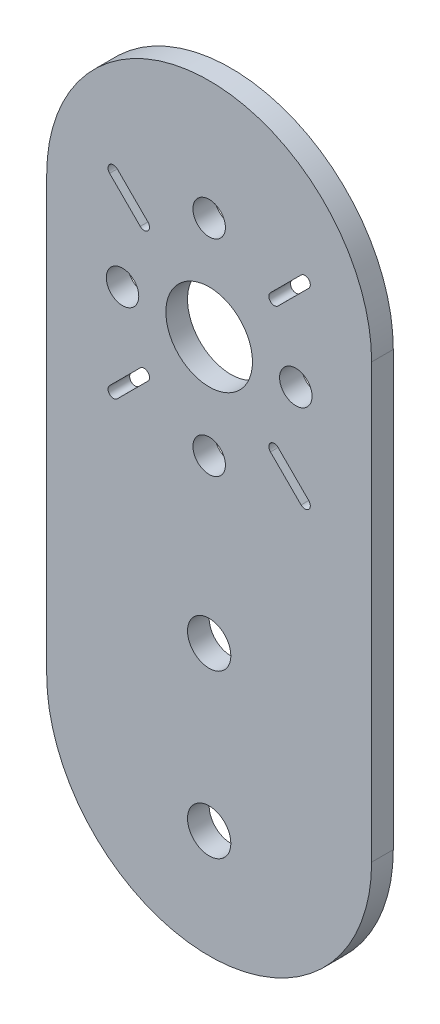
SolidWorks part; units mm, degrees
ref_plane "Front Plane" through (0, 0, 0) normal (0, 0, 1) x (1, 0, 0)
ref_plane "Top Plane" through (0, 0, 0) normal (0, 1, 0) x (1, 0, 0)
ref_plane "Right Plane" through (0, 0, 0) normal (1, 0, 0) x (0, 0, -1)
sketch "Sketch1" plane through (0, 0, 0) normal (0, 0, 1) x (1, 0, 0)
  line L2 (-15, 20) -> (-15, -20)
  line L4 (15, 20) -> (15, -20)
  line L6 (5.6569, 8.136) -> (8.4853, 5.3076)
  line L7 (6.364, 8.8431) -> (9.1924, 6.0147)
  line L8 (-6.364, 8.8431) -> (-9.1924, 6.0147)
  line L11 (6.364, 20.1569) -> (9.1924, 22.9853)
  line L12 (5.6569, 20.864) -> (8.4853, 23.6924)
  line L13 (-5.6569, 8.136) -> (-8.4853, 5.3076)
  line L14 (-5.6569, 20.864) -> (-8.4853, 23.6924)
  line L15 (-6.364, 20.1569) -> (-9.1924, 22.9853)
  arc A0 (15, 20) -> (-15, 20) centre (0, 20) ccw
  arc A1 (-15, -20) -> (15, -20) centre (0, -20) ccw
  circle A2 centre (0, -25) radius 2
  circle A3 centre (0, -10) radius 2
  circle A4 centre (0, 5) radius 1.5
  circle A5 centre (0, 24) radius 1.5
  circle A6 centre (-8, 14.5) radius 1.5
  circle A7 centre (8, 14.5) radius 1.5
  circle A8 centre (0, 14.5) radius 4
  arc A9 (5.6569, 20.864) -> (6.364, 20.1569) centre (6.0104, 20.5104) ccw
  arc A10 (9.1924, 22.9853) -> (8.4853, 23.6924) centre (8.8388, 23.3388) ccw
  arc A11 (6.364, 8.8431) -> (5.6569, 8.136) centre (6.0104, 8.4896) ccw
  arc A12 (8.4853, 5.3076) -> (9.1924, 6.0147) centre (8.8388, 5.6612) ccw
  arc A13 (-5.6569, 8.136) -> (-6.364, 8.8431) centre (-6.0104, 8.4896) ccw
  arc A14 (-9.1924, 6.0147) -> (-8.4853, 5.3076) centre (-8.8388, 5.6612) ccw
  arc A15 (-6.364, 20.1569) -> (-5.6569, 20.864) centre (-6.0104, 20.5104) ccw
  arc A16 (-8.4853, 23.6924) -> (-9.1924, 22.9853) centre (-8.8388, 23.3388) ccw
  point P0 (0, 0)
  point P10 (0, -35)
  point P24 (10.6066, 25.1066)
  point P25 (0.3536, 14.1464)
  point P26 (10.9602, 24.753)
  point P27 (-0.3536, 14.8536)
  point P28 (10.253, 25.4602)
  dimension "D3" = 10
  dimension "D4" = 15
  dimension "D5" = 15
  dimension "D7" = 16
  dimension "D9" = 4
  dimension "D1" = 30
  dimension "D2" = 40
  dimension "D6" = 19
extrude "Boss-Extrude1" add sketch "Sketch1" along normal blind 2
